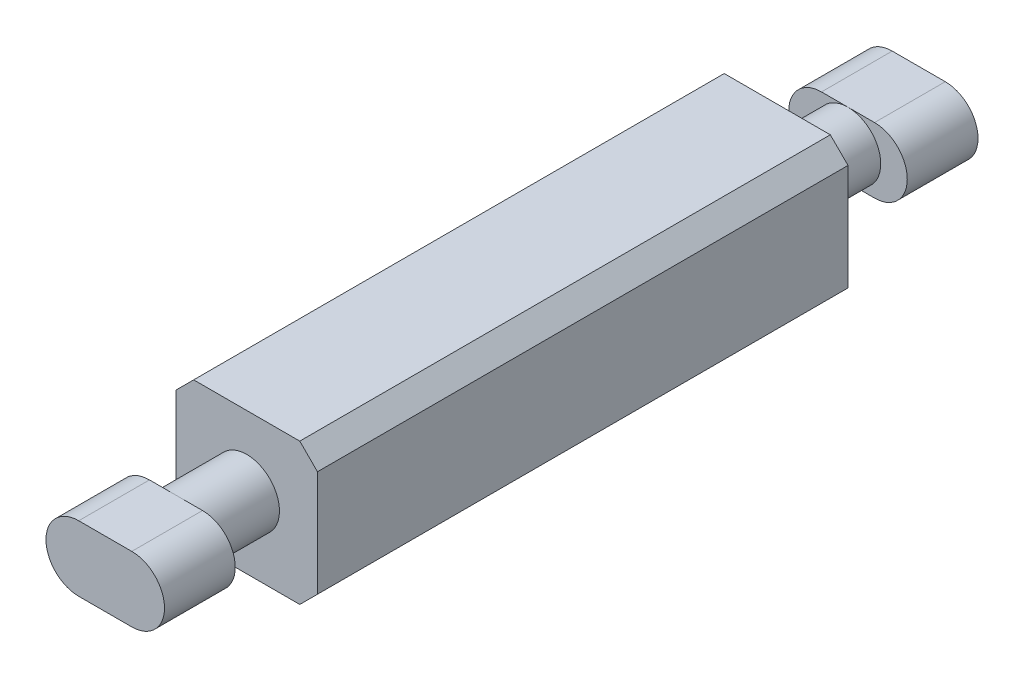
SolidWorks part; units mm, degrees
material "ABS"
ref_plane "Front Plane" through (0, 0, 0) normal (0, 0, 1) x (1, 0, 0)
ref_plane "Top Plane" through (0, 0, 0) normal (0, 1, 0) x (1, 0, 0)
ref_plane "Right Plane" through (0, 0, 0) normal (1, 0, 0) x (0, 0, -1)
sketch "Sketch1" plane through (0, 0, 0) normal (0, 1, 0) x (1, 0, 0)
  line L1 (-2, -7.5) -> (2, -7.5)
  line L2 (-2, -7.5) -> (-2, 7.5)
  line L3 (-2, 7.5) -> (2, 7.5)
  line L4 (2, -7.5) -> (2, 7.5)
  line L5 (-2, -7.5) -> (2, 7.5) construction
  line L6 (-2, 7.5) -> (2, -7.5) construction
  point P0 (0, 0)
  dimension "D1" = 15
  dimension "D2" = 4
extrude "Boss-Extrude1" add sketch "Sketch1" along normal blind 4
sketch "Sketch2" plane through (0, 0, 7.5) normal (0, 0, 1) x (1, 0, 0)
  line L3 (0, 0) -> (0, 4) construction
  line L4 (-2, 4) -> (2, 4) construction
  line L5 (-2, 2) -> (2, 2) construction
  line L6 (-2, 4) -> (-2, 0) construction
  line L7 (2, 4) -> (2, 0) construction
  circle A2 centre (0, 2) radius 0.925
  dimension "D1" = 1.85
extrude "Boss-Extrude2" add sketch "Sketch2" along normal blind 2 and the other way blind 17
chamfer "Chamfer1" distance 0.5 angle 45 4 edges at (-2, 0, 0) (-2, 4, 0) (2, 0, 0) (2, 4, 0)
sketch "Sketch3" plane through (0, 0, 9.5) normal (0, 0, 1) x (1, 0, 0)
  line L0 (-0.75, 2) -> (0.75, 2) construction
  line L1 (-0.75, 2.925) -> (0.75, 2.925)
  line L2 (-0.75, 1.075) -> (0.75, 1.075)
  arc A0 (-0.75, 2.925) -> (-0.75, 1.075) centre (-0.75, 2) ccw
  arc A1 (0.75, 1.075) -> (0.75, 2.925) centre (0.75, 2) ccw
  point P2 (0, 2)
  dimension "D1" = 1.85
  dimension "D2" = 0.75
extrude "Boss-Extrude3" add sketch "Sketch3" along normal blind 2
sketch "Sketch4" plane through (0, 0, -9.5) normal (0, 0, -1) x (-1, 0, 0)
  line L0 (-0.75, 2) -> (0.75, 2) construction
  line L1 (-0.75, 2.925) -> (0.75, 2.925)
  line L2 (-0.75, 1.075) -> (0.75, 1.075)
  arc A0 (-0.75, 2.925) -> (-0.75, 1.075) centre (-0.75, 2) ccw
  arc A1 (0.75, 1.075) -> (0.75, 2.925) centre (0.75, 2) ccw
  point P2 (0, 2)
  dimension "D1" = 1.85
  dimension "D2" = 0.75
extrude "Boss-Extrude4" add sketch "Sketch4" along normal blind 2
